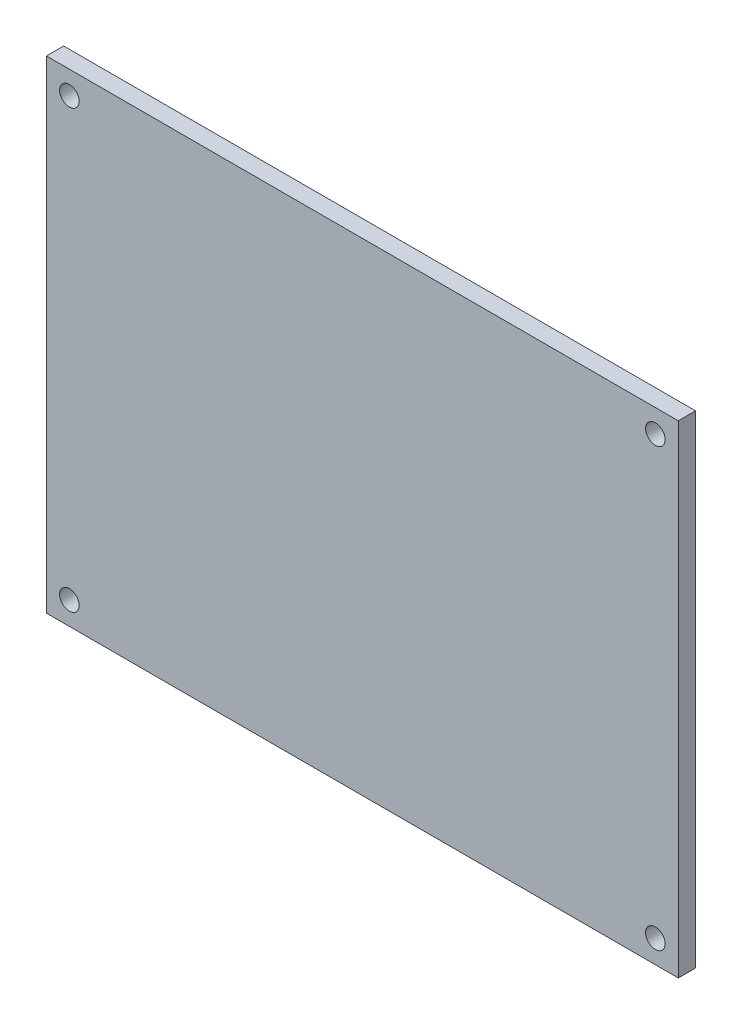
SolidWorks part; units mm, degrees
ref_plane "前视基准面" through (0, 0, 0) normal (0, 0, 1) x (1, 0, 0)
ref_plane "上视基准面" through (0, 0, 0) normal (0, 1, 0) x (1, 0, 0)
ref_plane "右视基准面" through (0, 0, 0) normal (1, 0, 0) x (0, 0, -1)
sketch "草图1" plane through (0, 0, 0) normal (0, 0, 1) x (1, 0, 0)
  line L1 (-52.1294, 35.0209) -> (57.8706, 35.0209)
  line L2 (-52.1294, 35.0209) -> (-52.1294, -48.9791)
  line L3 (-52.1294, -48.9791) -> (57.8706, -48.9791)
  line L4 (57.8706, 35.0209) -> (57.8706, -48.9791)
  circle A0 centre (-48.1294, 31.0209) radius 1.7
  circle A1 centre (53.8706, 31.0209) radius 1.7
  circle A2 centre (53.8706, -44.9791) radius 1.7
  circle A3 centre (-48.1294, -44.9791) radius 1.7
  dimension "D7" = 3.4
  dimension "D8" = 3.4
  dimension "D9" = 3.4
  dimension "D10" = 3.4
  dimension "D1" = 110
  dimension "D2" = 84
extrude "凸台-拉伸1" add sketch "草图1" along normal blind 3
